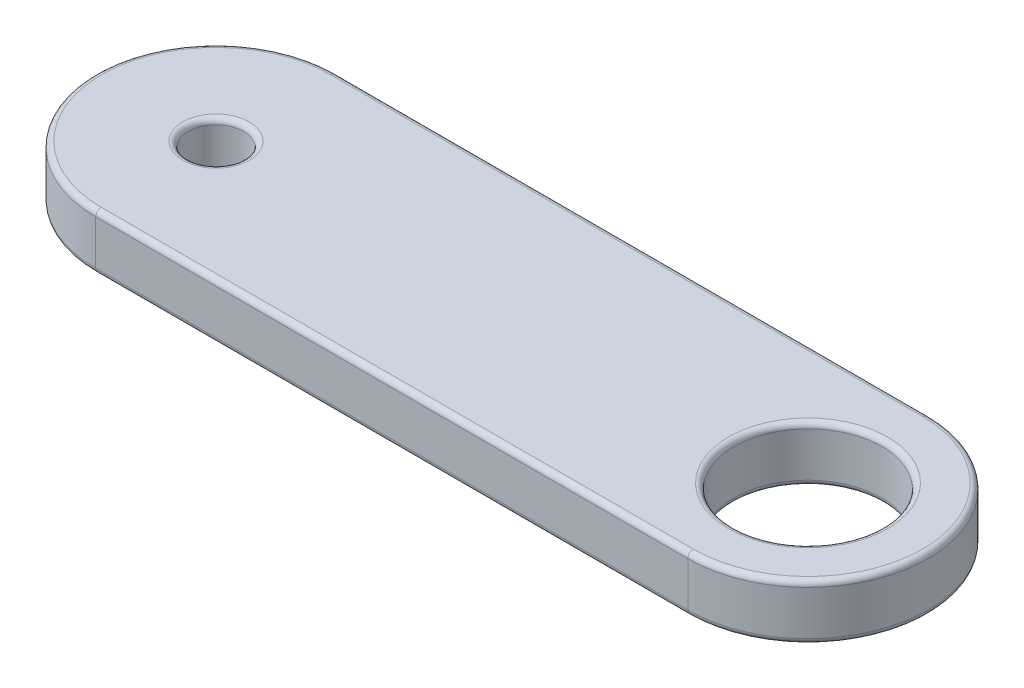
SolidWorks part; units mm, degrees
material "Balsa"
ref_plane "Front Plane" through (0, 0, 0) normal (0, 0, 1) x (1, 0, 0)
ref_plane "Top Plane" through (0, 0, 0) normal (0, 1, 0) x (1, 0, 0)
ref_plane "Right Plane" through (0, 0, 0) normal (1, 0, 0) x (0, 0, -1)
sketch "Sketch1" plane through (0, 0, 0) normal (0, 1, 0) x (1, 0, 0)
  line L0 (-8, 0) -> (8, 0) construction
  line L1 (-8, 3.25) -> (8, 3.25)
  line L2 (-8, -3.25) -> (8, -3.25)
  arc A0 (-8, 3.25) -> (-8, -3.25) centre (-8, 0) ccw
  arc A1 (8, -3.25) -> (8, 3.25) centre (8, 0) ccw
  circle A2 centre (-8, 0) radius 0.75
  circle A3 centre (8, 0) radius 2
  point P3 (0, 0)
  dimension "D1" = 1.5
  dimension "D3" = 6.5
  dimension "D4" = 4
  dimension "D2" = 16
extrude "Boss-Extrude1" add sketch "Sketch1" along normal mid plane 1.5
fillet "Fillet1" radius 0.15 12 edges at (8, -0.75, 2) (-8, -0.75, 0.75) (0, -0.75, 3.25) (11.25, -0.75, 0) (0, -0.75, -3.25) (-11.25, -0.75, 0) (8, 0.75, 2) (0, 0.75, -3.25) (11.25, 0.75, 0) (0, 0.75, 3.25) (-11.25, 0.75, 0) (-8, 0.75, 0.75)
